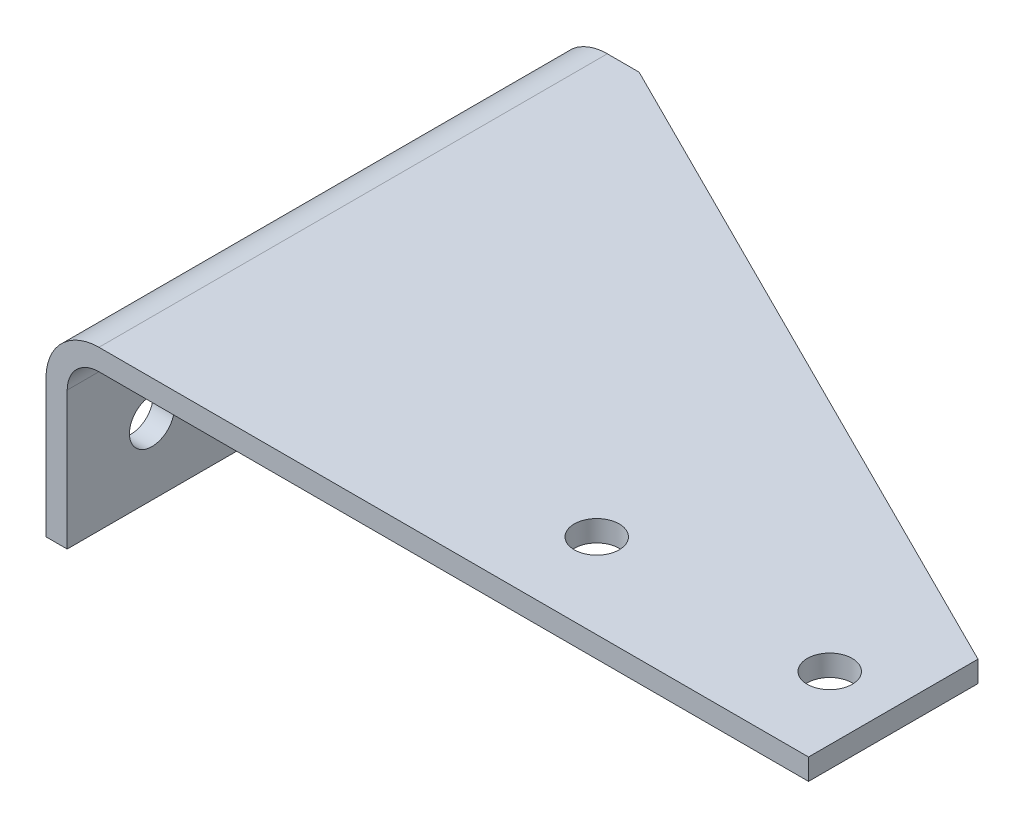
SolidWorks part; units mm, degrees
material "ASTM A36"
ref_plane "Front" through (0, 0, 0) normal (0, 0, 1) x (1, 0, 0)
ref_plane "Top" through (0, 0, 0) normal (0, 1, 0) x (1, 0, 0)
ref_plane "Side" through (0, 0, 0) normal (1, 0, 0) x (0, 0, -1)
sketch "Sketch1" plane through (0, 0, 0) normal (0, 0, 1) x (1, 0, 0)
  line L0 (228.6, 0) -> (15.875, 0)
  line L1 (0, -15.875) -> (0, -57.15)
  line L2 (0, -57.15) -> (6.35, -57.15)
  line L3 (6.35, -57.15) -> (6.35, -15.875)
  line L4 (15.875, -6.35) -> (228.6, -6.35)
  line L5 (228.6, -6.35) -> (228.6, 0)
  line L6 (50, 0) -> (-50, 0) construction
  arc A0 (15.875, 0) -> (0, -15.875) centre (15.875, -15.875) ccw
  arc A1 (6.35, -15.875) -> (15.875, -6.35) centre (15.875, -15.875) cw
  dimension "D3" = 9.525
  dimension "D1" = 228.6
  dimension "D2" = 57.15
  dimension "D4" = 6.35
extrude "Extrude1" add sketch "Sketch1" against normal mid plane 254
sketch "Sketch2" plane through (0, 0, 0) normal (0, 1, 0) x (1, 0, 0)
  line L0 (25.4, 127) -> (228.6, 25.4)
  line L1 (228.6, 127) -> (15.875, 127) construction
  line L2 (228.6, 127) -> (228.6, -127) construction
  line L3 (0, -50) -> (0, 50) construction
  line L4 (-50, 0) -> (50, 0) construction
  line L5 (0, 0) -> (258.8616, 0) construction
  line L6 (228.6, 25.4) -> (228.6, 127)
  line L7 (228.6, 127) -> (25.4, 127)
  line L8 (25.4, -127) -> (228.6, -25.4)
  line L9 (228.6, -127) -> (25.4, -127)
  line L10 (228.6, -25.4) -> (228.6, -127)
  line L11 (0, 0) -> (139.7, 0) construction
  line L12 (139.7, 0) -> (209.55, 0) construction
  circle A2 centre (209.55, 0) radius 6.731
  circle A3 centre (139.7, 0) radius 6.731
  dimension "D5" = 69.85
  dimension "D6" = 13.462
  dimension "D1" = 25.4
  dimension "D2" = 25.4
  dimension "D3" = 25.4
  dimension "D4" = 139.7
extrude "Cut-Chamfer" cut sketch "Sketch2" along normal blind 508 and the other way through all
sketch "Sketch3" plane through (0, 0, 0) normal (1, 0, 0) x (0, 0, -1)
  line L0 (101.6, -36.5125) -> (0, -36.5125) construction
  line L2 (50, 0) -> (-50, 0) construction
  line L3 (-14.7043, -93.6625) -> (186.8542, -93.6625) construction
  line L4 (0, 50) -> (0, -50) construction
  line L5 (0, -36.5125) -> (-101.6, -36.5125) construction
  line L6 (-101.6, -36.5125) -> (-101.6, -150.8125) construction
  line L7 (-101.6, -150.8125) -> (0, -150.8125) construction
  circle A0 centre (0, -36.5125) radius 6.731
  circle A1 centre (101.6, -36.5125) radius 6.731
  circle A2 centre (0, -150.8125) radius 6.731
  circle A3 centre (101.6, -150.8125) radius 6.731
  circle A4 centre (-101.6, -36.5125) radius 6.731
  circle A5 centre (-101.6, -150.8125) radius 6.731
  dimension "D2" = 101.6
  dimension "D3" = 13.462
  dimension "D1" = 101.6
  dimension "D4" = 36.5125
  dimension "D5" = 93.6625
extrude "Cut-Holes" cut sketch "Sketch3" along normal through all
sketch "Sketch5" plane through (0, 0, 0) normal (0, 1, 0) x (1, 0, 0)
  line L0 (-7.3488, -25.4) -> (228.6, -25.4)
  line L1 (228.6, 25.4) -> (228.6, -25.4) construction
  dimension "D1" = 25.4
  dimension "D2" = 235.9488
extrude "Cut LH -001" cut sketch "Sketch5" against normal through all flip side to cut
sketch "Sketch4" plane through (0, 0, 0) normal (0, 1, 0) x (1, 0, 0)
  line L0 (-9.6314, 25.4) -> (228.6, 25.4)
  line L1 (228.6, 25.4) -> (228.6, -25.4) construction
  dimension "D1" = 25.4
  dimension "D2" = 238.2314
extrude "Cut RH -002" [suppressed] cut sketch "Sketch4" against normal through all
